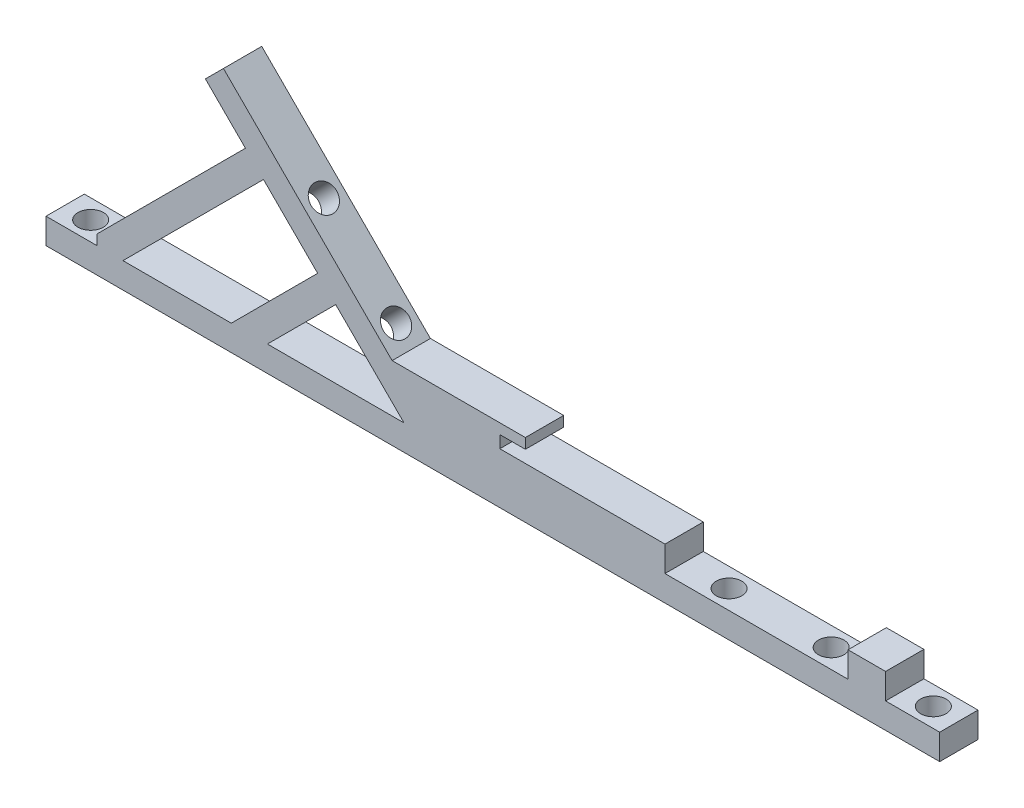
SolidWorks part; units mm, degrees
ref_plane "Front Plane" through (0, 0, 0) normal (0, 0, 1) x (1, 0, 0)
ref_plane "Top Plane" through (0, 0, 0) normal (0, 1, 0) x (1, 0, 0)
ref_plane "Right Plane" through (0, 0, 0) normal (1, 0, 0) x (0, 0, -1)
sketch "Sketch1" plane through (0, 0, 0) normal (0, 1, 0) x (1, 0, 0)
  line L1 (-82.55, -2.3813) -> (3.175, -2.3813)
  line L2 (-82.55, -2.3813) -> (-82.55, 2.3813)
  line L3 (-82.55, 2.3813) -> (3.175, 2.3813)
  line L4 (3.175, -2.3813) -> (3.175, 2.3813)
  circle A0 centre (0, 0) radius 1.5875
  circle A1 centre (-79.375, 0) radius 1.5875
  point P9 (0, 0)
  point P10 (3.175, 0)
  dimension "D2" = 3.175
  dimension "D1" = 79.375
  dimension "D3" = 3.175
  dimension "D4" = 3.175
  dimension "D5" = 4.7625
extrude "Boss-Extrude1" add sketch "Sketch1" along normal blind 3.175
sketch "Sketch2" plane through (0, 0, 2.3813) normal (0, 0, 1) x (1, 0, 0)
  line L0 (-33.5438, 3.175) -> (-60.4846, 30.1158)
  line L1 (-82.55, 3.175) -> (3.175, 3.175) construction
  line L2 (-60.4846, 30.1158) -> (-62.7296, 27.8707)
  line L3 (-62.7296, 27.8707) -> (-38.0339, 3.175)
  line L4 (-38.0339, 3.175) -> (-33.5438, 3.175)
  line L5 (-52.7659, 7.6735) -> (-57.2644, 3.175) construction
  line L6 (-48.7717, 13.9128) -> (-59.5095, 3.175)
  line L7 (-46.5266, 11.6677) -> (-55.0194, 3.175)
  line L8 (-55.0194, 3.175) -> (-59.5095, 3.175)
  line L9 (-51.6434, 6.551) -> (-56.1419, 2.0525) construction
  line L10 (-53.8884, 8.7961) -> (-58.387, 4.2975) construction
  line L11 (-56.6294, 21.7705) -> (-75.2249, 3.175) construction
  line L12 (-57.752, 22.893) -> (-76.1855, 4.4595)
  line L13 (-55.5069, 20.648) -> (-72.9799, 3.175)
  line L14 (-72.9799, 3.175) -> (-76.1855, 3.175)
  line L15 (-57.752, 22.893) -> (-76.3475, 4.2975) construction
  line L16 (-55.5069, 20.648) -> (-74.1024, 2.0525) construction
  line L18 (-76.1855, 4.4595) -> (-76.1855, 3.175)
  line L19 (-5.5843, 3.175) -> (-37.3343, 3.175)
  line L20 (-5.5843, 3.175) -> (-5.5843, 6.35)
  line L21 (-5.5843, 6.35) -> (-37.3343, 6.35)
  line L22 (-37.3343, 3.175) -> (-37.3343, 6.35)
  line L23 (-26.118, 6.35) -> (-38.75, 6.35)
  line L24 (-26.118, 6.35) -> (-26.118, 7.874)
  line L25 (-26.118, 7.874) -> (-38.75, 7.874)
  line L26 (-38.75, 6.35) -> (-38.75, 7.874)
  line L27 (-39.9867, 7.874) -> (-22.943, 7.874)
  line L28 (-39.9867, 7.874) -> (-39.9867, 9.144)
  line L29 (-39.9867, 9.144) -> (-22.943, 9.144)
  line L30 (-22.943, 7.874) -> (-22.943, 9.144)
  point P38 (-22.943, 8.509)
  line M8 (3.175, 3.175) -> (-82.55, 3.175)
  dimension "D3" = 3.175
  dimension "D4" = 38.1
  dimension "D6" = 45
  dimension "D7" = 12.7
  dimension "D11" = 3.175
  dimension "D12" = 31.75
  dimension "D13" = 1.524
  dimension "D14" = 1.27
  dimension "D15" = 3.175
  dimension "D1" = 1.5875
  dimension "D2" = 1.5875
  dimension "D8" = 1.5875
  dimension "D9" = 1.5875
extrude "Boss-Extrude2" add sketch "Sketch2" against normal blind 4.7625 contours L2 L3 L0 M8 | L7 L3 L6 M8 | L13 L3 L12 M8 | L27 L30 L29 L0 | L24 L25 L0 L21 | L20 L21 L0 M8 | L22 L0 L21 M8 | L26 L23 L21 L0 L25 | L29 L28 L27 L0
sketch "Sketch3" plane through (-15.1844, -15.1844, 0) normal (0.7071, 0.7071, 0) x (0, 0, -1)
  line L0 (2.3813, 25.9641) -> (-2.3813, 25.9641) construction
  line L1 (2.3813, 64.0641) -> (-2.3813, 64.0641) construction
  circle A0 centre (0, 49.7766) radius 1.5875
  circle A1 centre (0, 37.0766) radius 1.5875
  point P8 (0, 64.0641)
  dimension "D3" = 3.175
  dimension "D1" = 12.7
  dimension "D2" = 11.1125
extrude "Cut-Extrude1" cut sketch "Sketch3" against normal up to next contours A0 | A1
sketch "Sketch4" plane through (3.175, 0, 0) normal (1, 0, 0) x (0, 0, -1)
  line L8 (-2.3813, 0) -> (2.3813, 0)
  line L9 (2.3813, 0) -> (2.3813, 3.175)
  line L10 (2.3813, 3.175) -> (-2.3813, 3.175)
  line L11 (-2.3813, 3.175) -> (-2.3813, 0)
  line L12 (-2.3813, 0) -> (2.3813, 0)
  line L13 (2.3813, 0) -> (2.3813, 3.175)
  line L14 (2.3813, 3.175) -> (-2.3813, 3.175)
  line L15 (-2.3813, 3.175) -> (-2.3813, 0)
  dimension "D1" = 0
extrude "Boss-Extrude3" add sketch "Sketch4" along normal blind 25.4
sketch "Sketch5" plane through (0, 3.175, 0) normal (0, 1, 0) x (1, 0, 0)
  line L0 (-5.5843, -2.3813) -> (28.575, -2.3813) construction
  circle A0 centre (12.7, 0) radius 1.5875
  circle A1 centre (25.4, 0) radius 1.5875
  point P4 (0, 0)
  dimension "D3" = 3.175
  dimension "D1" = 12.7
  dimension "D2" = 12.7
  dimension "D4" = 2.3813
extrude "Cut-Extrude2" cut sketch "Sketch5" against normal through all
sketch "Sketch6" plane through (0, 0, 2.3813) normal (0, 0, 1) x (1, 0, 0)
  line L0 (-5.5843, 3.175) -> (28.575, 3.175) construction
  line L1 (17.1793, 3.175) -> (21.8465, 3.175)
  line L2 (17.1793, 3.175) -> (17.1793, 6.35)
  line L3 (17.1793, 6.35) -> (21.8465, 6.35)
  line L4 (21.8465, 3.175) -> (21.8465, 6.35)
  line L5 (-5.5843, 6.35) -> (-26.118, 6.35) construction
extrude "Boss-Extrude4" add sketch "Sketch6" against normal blind 4.7625
